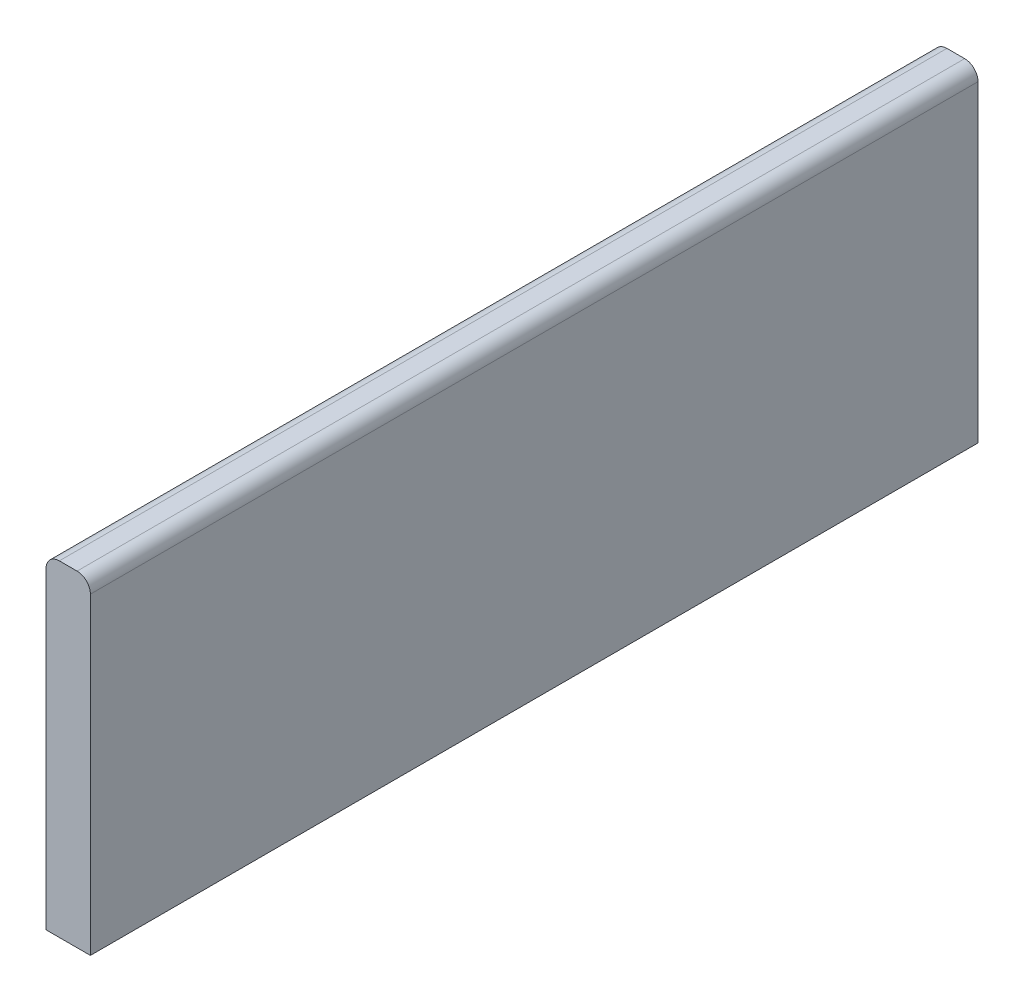
SolidWorks part; units mm, degrees
ref_plane "Plan de face" through (0, 0, 0) normal (0, 0, 1) x (1, 0, 0)
ref_plane "Plan de dessus" through (0, 0, 0) normal (0, 1, 0) x (1, 0, 0)
ref_plane "Plan de droite" through (0, 0, 0) normal (1, 0, 0) x (0, 0, -1)
sketch "Esquisse1" plane through (0, 0, 0) normal (0, 0, 1) x (1, 0, 0)
  line L0 (261, 0) -> (-201, 0) construction
  line L1 (104, 0) -> (114, 0)
  line L2 (104, 0) -> (104, -73.5)
  line L3 (104, -73.5) -> (114, -73.5)
  line L4 (114, 0) -> (114, -73.5)
  line L5 (261, -73.5) -> (-201, -73.5) construction
  line L6 (261, -73.5) -> (261, 0) construction
  dimension "D1" = 147
  dimension "D2" = 10
extrude "Boss.-Extru.1" add sketch "Esquisse1" along normal blind 200 contours L2 L3 L4 L1
fillet "Congé1" radius 3 2 edges at (114, 0, 100) (104, 0, 100)
